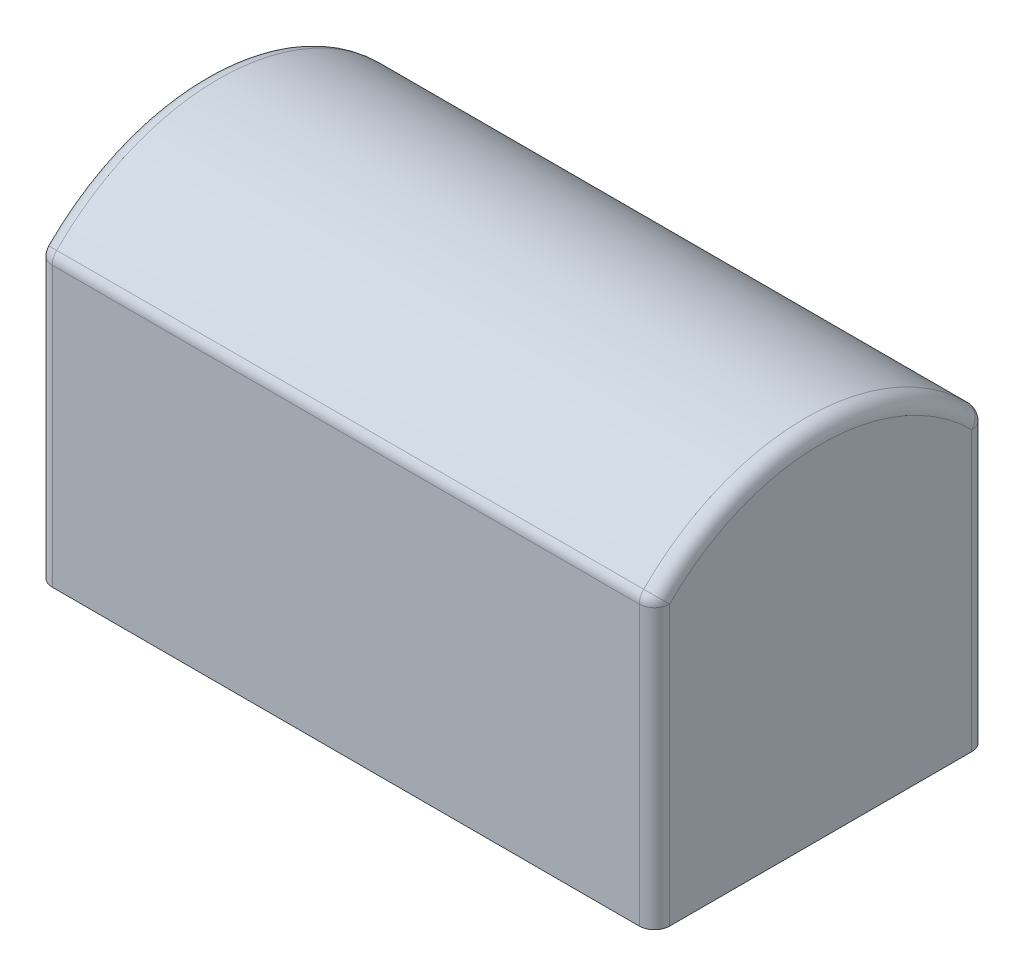
SolidWorks part; units mm, degrees
material "PE High Density"
ref_plane "Front Plane" through (0, 0, 0) normal (0, 0, 1) x (1, 0, 0)
ref_plane "Top Plane" through (0, 0, 0) normal (0, 1, 0) x (1, 0, 0)
ref_plane "Right Plane" through (0, 0, 0) normal (1, 0, 0) x (0, 0, -1)
sketch "Sketch1" plane through (0, 0, 0) normal (1, 0, 0) x (0, 0, -1)
  line L0 (-2.7781, 0) -> (2.7781, 0)
  line L1 (2.7781, 0) -> (2.7781, 4.7625)
  line L2 (-2.7781, 0) -> (-2.7781, 4.7625)
  arc A0 (2.7781, 4.7625) -> (-2.7781, 4.7625) centre (0, 2.159) ccw
  point P4 (0, 0)
  dimension "D1" = 4.7625
  dimension "D2" = 5.5562
  dimension "D4" = 2.159
extrude "Boss-Extrude1" add sketch "Sketch1" along normal blind 10.3187
fillet "Fillet1" radius 0.254 8 edges at (0, 2.3813, -2.7781) (5.1594, 4.7625, -2.7781) (0, 2.3813, 2.7781) (0, 5.9664, 0) (10.3187, 5.9664, 0) (10.3187, 2.3813, -2.7781) (5.1594, 4.7625, 2.7781) (10.3187, 2.3813, 2.7781)
